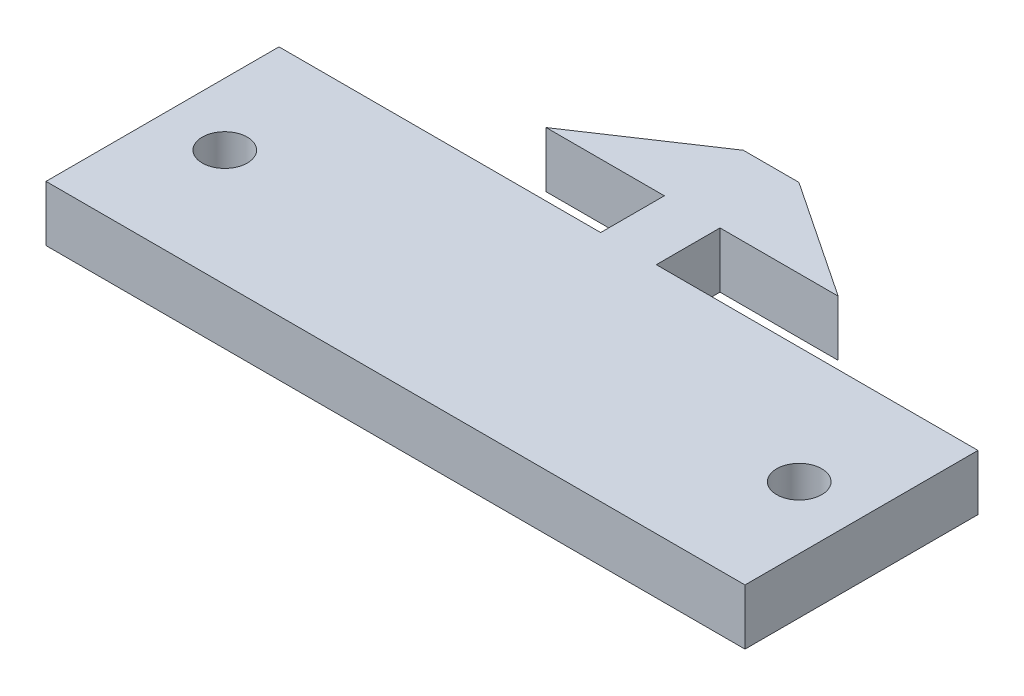
SolidWorks part; units mm, degrees
ref_plane "Front" through (0, 0, 0) normal (0, 0, 1) x (1, 0, 0)
ref_plane "Top" through (0, 0, 0) normal (0, 1, 0) x (1, 0, 0)
ref_plane "Right" through (0, 0, 0) normal (1, 0, 0) x (0, 0, -1)
sketch "Sketch1" plane through (0, 0, 0) normal (0, 1, 0) x (1, 0, 0)
  line L0 (-1.7907, 2.05) -> (-9.398, 2.05)
  line L2 (-1.7907, -2.05) -> (-1.7907, 2.05)
  line L4 (1.7907, -2.05) -> (1.7907, 2.05)
  line L7 (-9.398, 2.05) -> (-1.7907, 7.13)
  line L8 (-1.7907, 7.13) -> (1.7907, 7.13)
  line L9 (1.7907, 7.13) -> (9.398, 2.05)
  line L10 (9.398, 2.05) -> (1.7907, 2.05)
  line L11 (1.7907, -2.05) -> (22.5, -2.05)
  line L12 (-1.7907, -2.05) -> (-22.5, -2.05)
  line L13 (-22.5, -2.05) -> (-22.5, -17.05)
  line L14 (-22.5, -17.05) -> (22.5, -17.05)
  line L15 (22.5, -17.05) -> (22.5, -2.05)
  line L16 (22.5, -2.05) -> (1.7907, -2.05)
  point P0 (0, 0)
  point P17 (0, 7.13)
  point P19 (0, -17.05)
  point P24 (1.7907, 0)
  dimension "D1" = 18.796
  dimension "D2" = 3.5814
  dimension "D3" = 45
  dimension "D4" = 15
  dimension "D5" = 5.08
  dimension "D7" = 4.1
extrude "Boss-Extrude1" add sketch "Sketch1" along normal blind 3.5814 contours L14 L15 L11 L4 L10 L9 L8 L7 L0 L2 L12 L13
sketch "Sketch2" plane through (0, 3.5814, 0) normal (0, 1, 0) x (1, 0, 0)
  line L0 (0, 0) -> (0, -15.3387) construction
  line L2 (-22.5, -2.05) -> (-22.5, -17.05) construction
  circle A0 centre (-18.49, -9.55) radius 1.45
  circle A1 centre (18.49, -9.55) radius 1.45
  point P11 (-22.5, -9.55)
  dimension "D1" = 2.9
  dimension "D2" = 18.49
extrude "Cut-Extrude1" cut sketch "Sketch2" against normal through all
